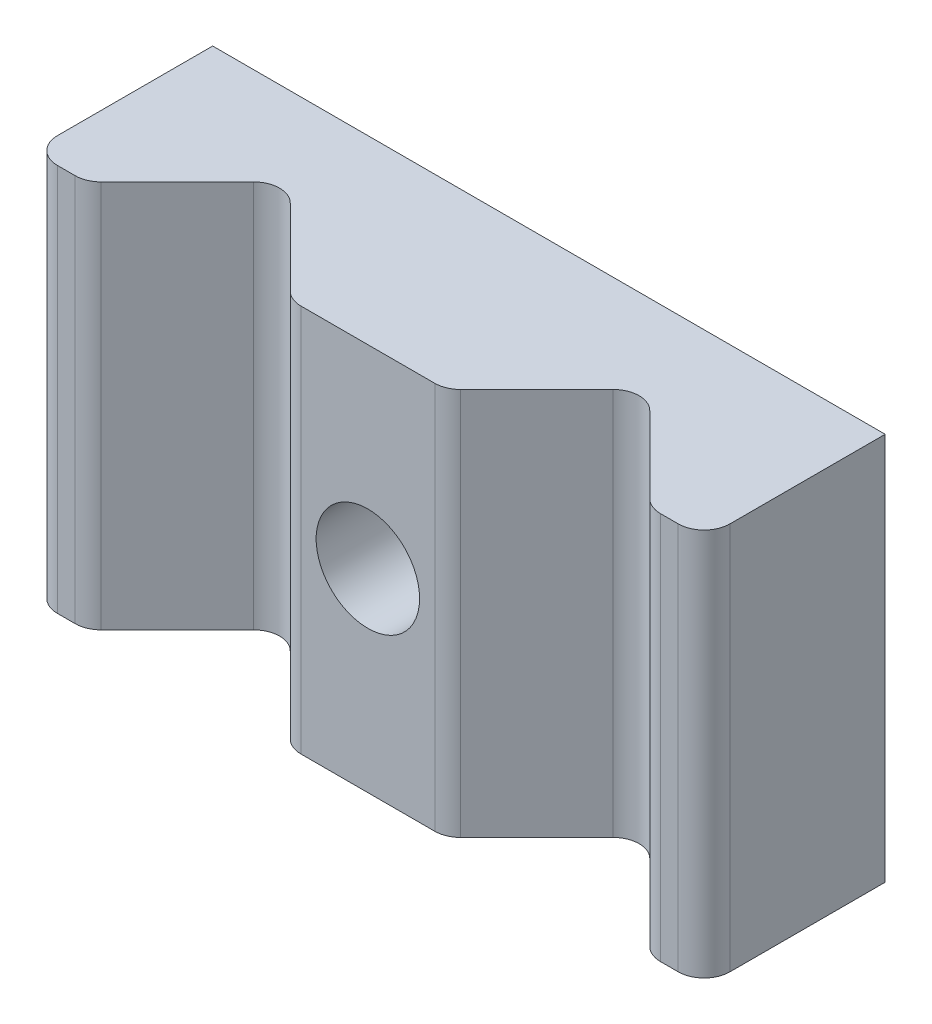
SolidWorks part; units mm, degrees
ref_plane "Front Plane" through (0, 0, 0) normal (0, 0, 1) x (1, 0, 0)
ref_plane "Top Plane" through (0, 0, 0) normal (0, 1, 0) x (1, 0, 0)
ref_plane "Right Plane" through (0, 0, 0) normal (1, 0, 0) x (0, 0, -1)
sketch "Sketch1" plane through (0, 0, 0) normal (0, 0, 1) x (1, 0, 0)
  line L0 (13, 15) -> (13, 0) construction
  line L1 (0, 0) -> (26, 0)
  line L2 (0, 0) -> (0, 15)
  line L3 (0, 15) -> (26, 15)
  line L4 (26, 0) -> (26, 15)
  circle A0 centre (13, 7.5) radius 2
  dimension "D1" = 4
  dimension "D2" = 26
  dimension "D3" = 15
extrude "Boss-Extrude1" add sketch "Sketch1" along normal blind 7
sketch "Sketch2" plane through (0, 15, 0) normal (0, 1, 0) x (1, 0, 0)
  line L0 (13, -7) -> (13, -8) construction
  line L1 (26, -7) -> (0, -7) construction
  line L2 (6.05, -8) -> (19.95, -8) construction
  line L3 (2.1003, -7) -> (5.3429, -3.7574)
  line L4 (6.7571, -3.7574) -> (9.9997, -7)
  line L5 (16.0003, -7) -> (19.2429, -3.7574)
  line L6 (20.6571, -3.7574) -> (23.8997, -7)
  line L7 (2.1003, -7) -> (9.9997, -7)
  line L8 (16.0003, -7) -> (23.8997, -7)
  circle A0 centre (6.05, -8) radius 3.5 construction
  circle A1 centre (19.95, -8) radius 3.5 construction
  arc A2 (19.2429, -3.7574) -> (20.6571, -3.7574) centre (19.95, -4.4645) cw
  arc A3 (5.3429, -3.7574) -> (6.7571, -3.7574) centre (6.05, -4.4645) cw
  dimension "D1" = 7
  dimension "D3" = 1
  dimension "D2" = 1
  dimension "D4" = 13.9
extrude "Cut-Extrude1" cut sketch "Sketch2" against normal through all
fillet "Fillet1" radius 1 6 edges at (0, 7.5, 7) (2.1003, 7.5, 7) (9.9997, 7.5, 7) (16.0003, 7.5, 7) (23.8997, 7.5, 7) (26, 7.5, 7)
